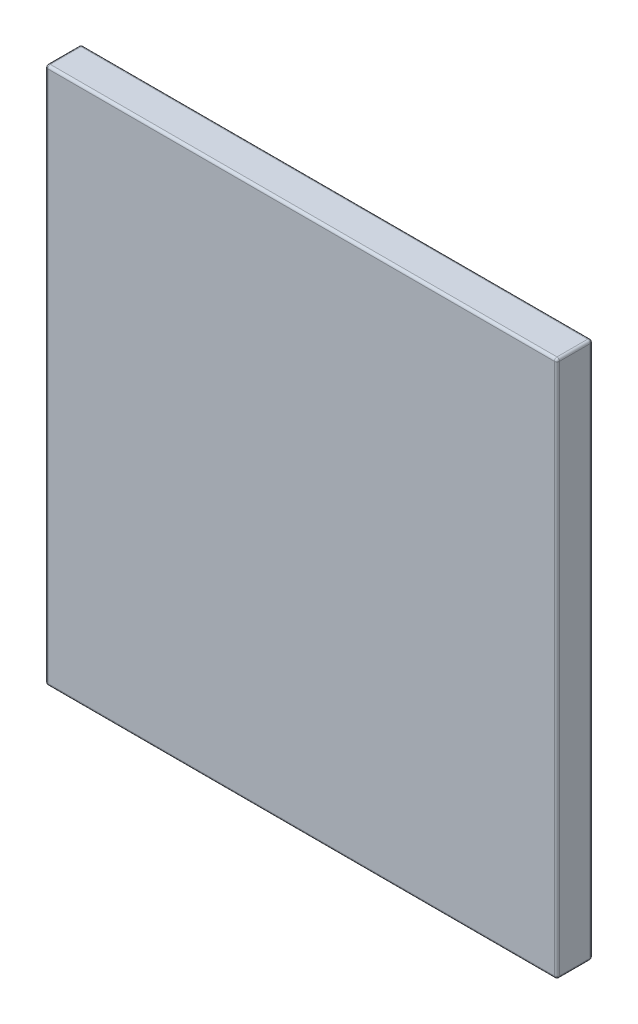
SolidWorks part; units mm, degrees
material "1060 Alloy"
ref_plane "Front Plane" through (0, 0, 0) normal (0, 0, 1) x (1, 0, 0)
ref_plane "Top Plane" through (0, 0, 0) normal (0, 1, 0) x (1, 0, 0)
ref_plane "Right Plane" through (0, 0, 0) normal (1, 0, 0) x (0, 0, -1)
sketch "Sketch1" plane through (0, 0, 0) normal (0, 0, 1) x (1, 0, 0)
  line L1 (-104.1345, 45.4146) -> (-4.1345, 45.4146)
  line L2 (-104.1345, 45.4146) -> (-104.1345, -59.5854)
  line L3 (-104.1345, -59.5854) -> (-4.1345, -59.5854)
  line L4 (-4.1345, 45.4146) -> (-4.1345, -59.5854)
  line L5 (-104.1345, 45.4146) -> (-4.1345, -59.5854) construction
  line L6 (-104.1345, -59.5854) -> (-4.1345, 45.4146) construction
  point P0 (-54.1345, -7.0854)
  dimension "D1" = 100
  dimension "D2" = 105
extrude "Boss-Extrude1" add sketch "Sketch1" along normal blind 7
fillet "Fillet1" radius 0.5 12 edges at (-104.1345, -59.5854, 3.5) (-4.1345, -59.5854, 3.5) (-54.1345, -59.5854, 0) (-4.1345, -7.0854, 0) (-4.1345, 45.4146, 3.5) (-54.1345, 45.4146, 0) (-104.1345, -7.0854, 0) (-104.1345, 45.4146, 3.5) (-54.1345, 45.4146, 7) (-4.1345, -7.0854, 7) (-54.1345, -59.5854, 7) (-104.1345, -7.0854, 7)
